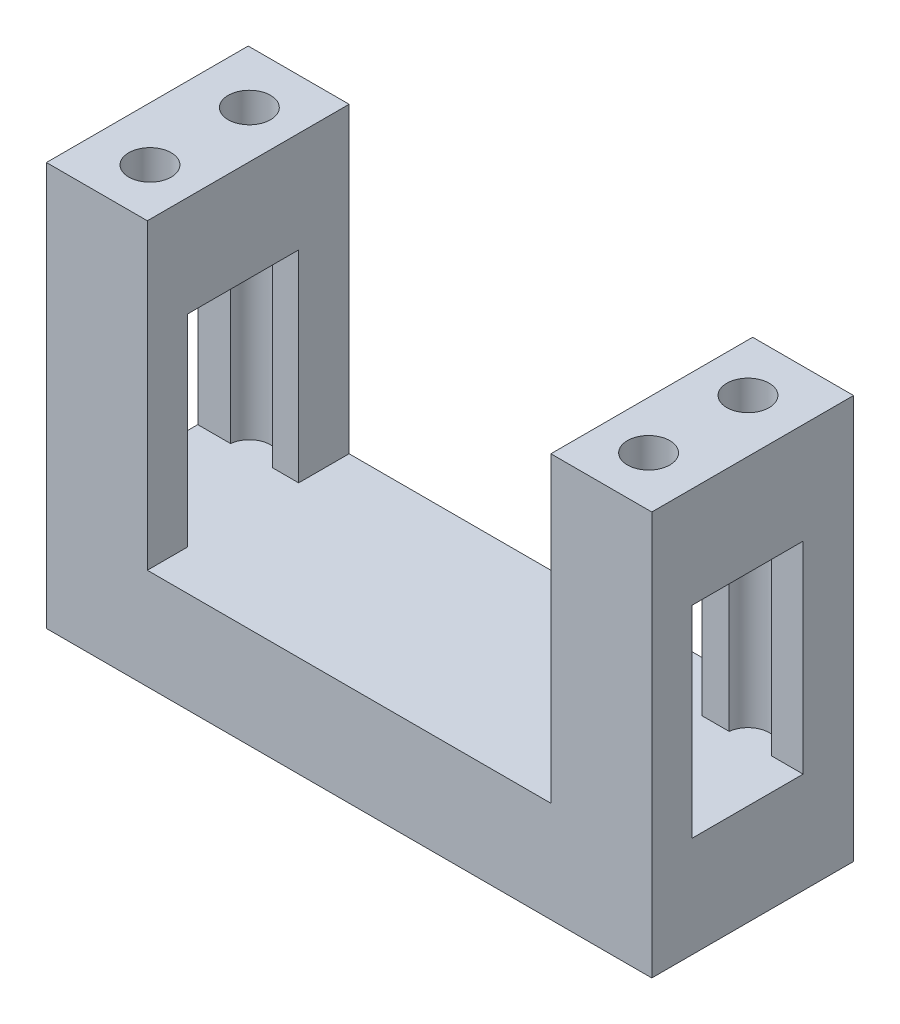
SolidWorks part; units mm, degrees
ref_plane "Ebene vorne" through (0, 0, 0) normal (0, 0, 1) x (1, 0, 0)
ref_plane "Ebene oben" through (0, 0, 0) normal (0, 1, 0) x (1, 0, 0)
ref_plane "Ebene rechts" through (0, 0, 0) normal (1, 0, 0) x (0, 0, -1)
sketch "Skizze1" plane through (0, 0, 0) normal (0, 0, 1) x (1, 0, 0)
  line L1 (0, 0) -> (60, 0)
  line L2 (0, 0) -> (0, 40)
  line L3 (0, 40) -> (60, 40)
  line L4 (60, 0) -> (60, 40)
  dimension "D1" = 60
  dimension "D2" = 40
extrude "Aufsatz-Linear austragen1" add sketch "Skizze1" along normal blind 20
sketch "Skizze2" plane through (0, 40, 0) normal (0, 1, 0) x (1, 0, 0)
  line L0 (60, 0) -> (0, 0) construction
  line L1 (10, 0) -> (50, 0)
  line L2 (10, 0) -> (10, -20)
  line L3 (10, -20) -> (50, -20)
  line L4 (50, 0) -> (50, -20)
  line L5 (60, -20) -> (0, -20) construction
  line L6 (0, -20) -> (0, 0) construction
  dimension "D1" = 40
  dimension "D2" = 10
extrude "Schnitt-Linear austragen1" cut sketch "Skizze2" against normal blind 30
sketch "Skizze3" plane through (60, 0, 0) normal (1, 0, 0) x (0, 0, -1)
  line L0 (-20, 0) -> (0, 0) construction
  line L1 (-16, 10) -> (-5, 10)
  line L2 (-16, 10) -> (-16, 30)
  line L3 (-16, 30) -> (-5, 30)
  line L4 (-5, 10) -> (-5, 30)
  line L5 (0, 0) -> (0, 40) construction
  dimension "D1" = 20
  dimension "D2" = 11
  dimension "D3" = 10
  dimension "D4" = 5
extrude "Schnitt-Linear austragen2" cut sketch "Skizze3" against normal through all
sketch "Skizze4" plane through (0, 40, 0) normal (0, 1, 0) x (1, 0, 0)
  line L0 (60, -20) -> (60, 0) construction
  line L1 (0, -20) -> (0, 0) construction
  line L2 (10, 0) -> (0, 0) construction
  line L3 (60, 0) -> (50, 0) construction
  line L4 (60, -20) -> (50, -20) construction
  line L5 (10, -20) -> (0, -20) construction
  circle A0 centre (5.3389, -5.225) radius 2.1
  circle A1 centre (5.3389, -15.075) radius 2.1
  circle A2 centre (54.7611, -15.075) radius 2.1
  circle A4 centre (54.7611, -5.225) radius 2.1
  dimension "D1" = 4.2
  dimension "D2" = 4.2
  dimension "D3" = 4.2
  dimension "D4" = 4.2
  dimension "D5" = 5.2389
  dimension "D6" = 5.2389
  dimension "D7" = 5.3389
  dimension "D8" = 5.3389
  dimension "D9" = 5.225
  dimension "D10" = 5.225
  dimension "D11" = 4.925
  dimension "D12" = 4.925
extrude "Schnitt-Linear austragen3" cut sketch "Skizze4" against normal up to surface (30 mm away) up to face at (30, 10, 10.3333)
